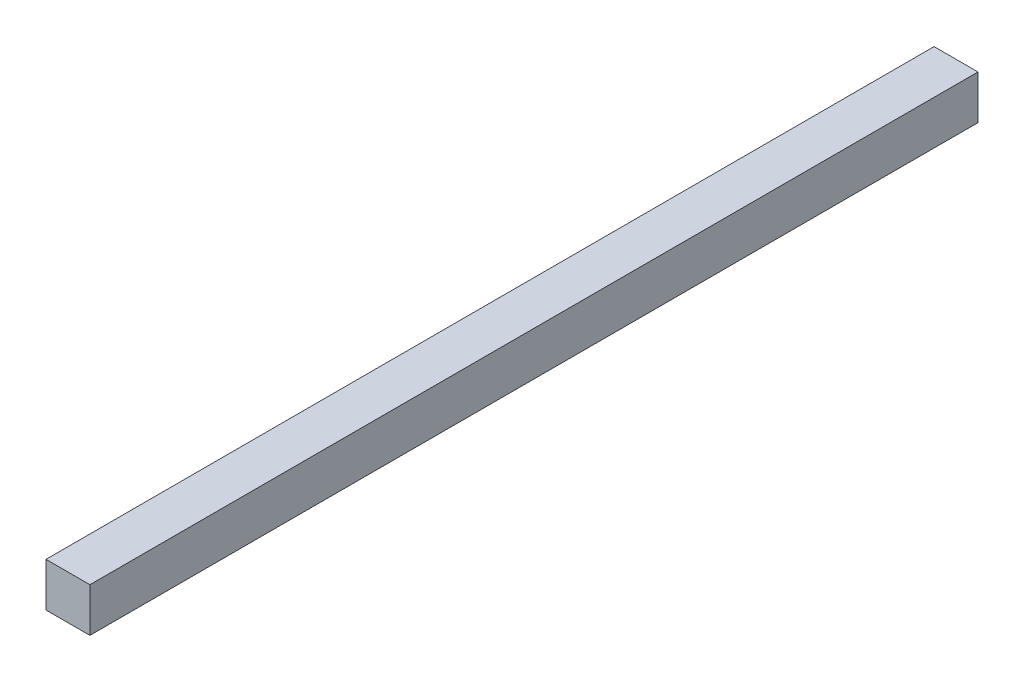
SolidWorks part; units mm, degrees
ref_plane "Front Plane" through (0, 0, 0) normal (0, 0, 1) x (1, 0, 0)
ref_plane "Top Plane" through (0, 0, 0) normal (0, 1, 0) x (1, 0, 0)
ref_plane "Right Plane" through (0, 0, 0) normal (1, 0, 0) x (0, 0, -1)
sketch "Sketch1" plane through (0, 0, 0) normal (0, 0, 1) x (1, 0, 0)
  line L1 (0, 0) -> (45, 0)
  line L2 (0, 0) -> (0, 45)
  line L3 (0, 45) -> (45, 45)
  line L4 (45, 0) -> (45, 45)
  dimension "D1" = 45
  dimension "D2" = 45
extrude "Boss-Extrude1" add sketch "Sketch1" along normal blind 910
